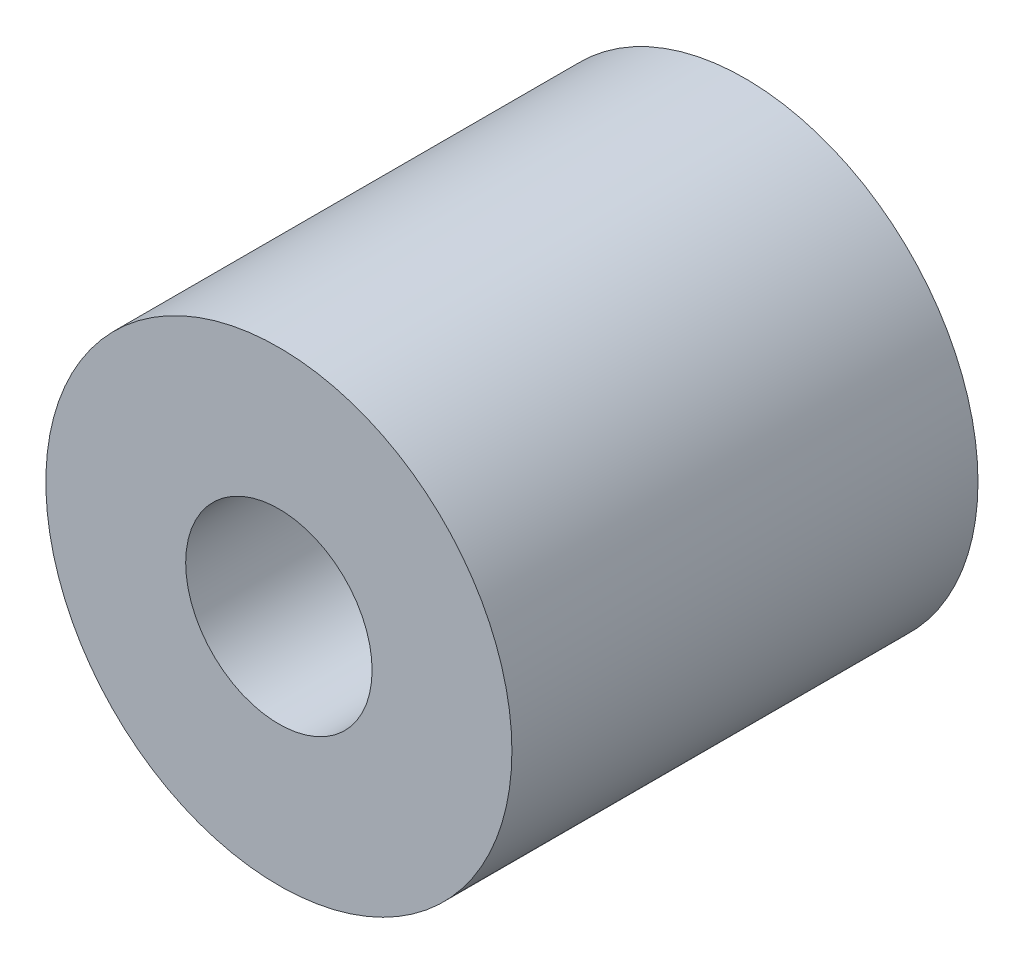
SolidWorks part; units mm, degrees
ref_plane "Plano frontal" through (0, 0, 0) normal (0, 0, 1) x (1, 0, 0)
ref_plane "Plano superior" through (0, 0, 0) normal (0, 1, 0) x (1, 0, 0)
ref_plane "Plano direito" through (0, 0, 0) normal (1, 0, 0) x (0, 0, -1)
sketch "Esboço1" plane through (0, 0, 0) normal (0, 0, 1) x (1, 0, 0)
  circle A0 centre (0, 0) radius 2
  circle A1 centre (0, 0) radius 5
extrude "Ressalto-extrusão1" add sketch "Esboço1" along normal blind 10
